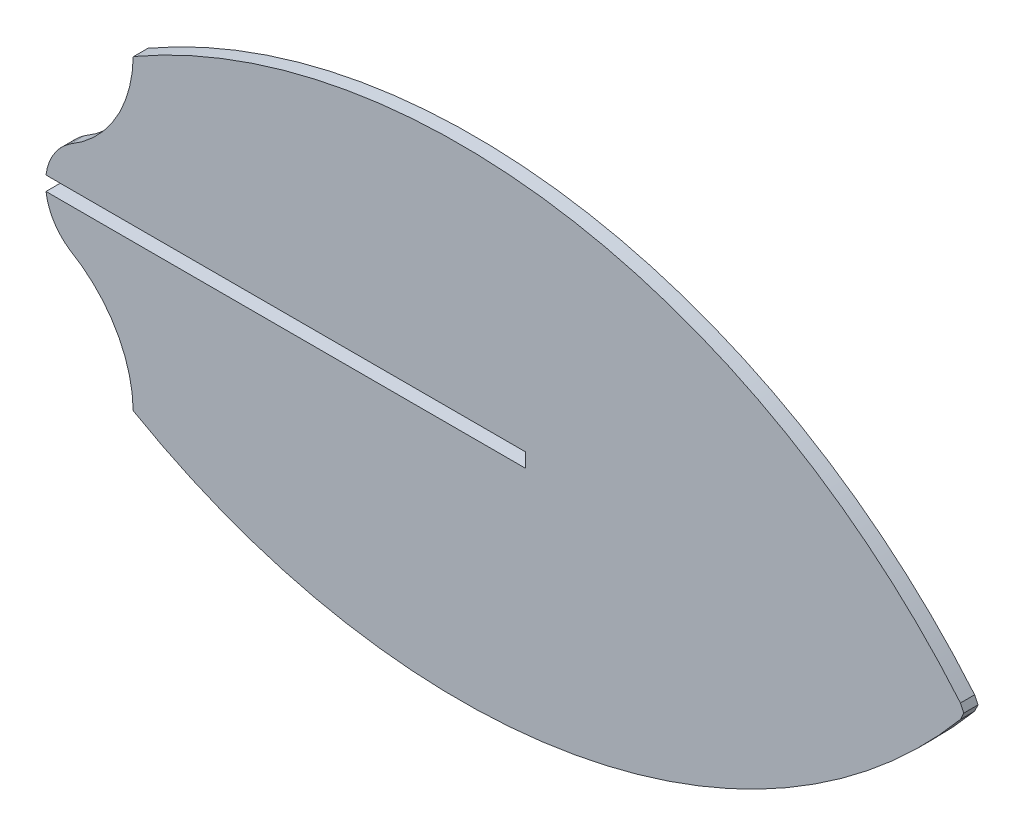
SolidWorks part; units mm, degrees
ref_plane "Front Plane" through (0, 0, 0) normal (0, 0, 1) x (1, 0, 0)
ref_plane "Top Plane" through (0, 0, 0) normal (0, 1, 0) x (1, 0, 0)
ref_plane "Right Plane" through (0, 0, 0) normal (1, 0, 0) x (0, 0, -1)
sketch "Sketch1" plane through (0, 0, 0) normal (0, 0, 1) x (1, 0, 0)
  line L0 (79.3572, 0) -> (79.3572, -1.524)
  line L2 (79.3572, 0) -> (27.9972, 0)
  line L3 (79.3572, -1.524) -> (79.3572, 0) construction
  line L4 (79.3572, -0.762) -> (126.3316, -0.762) construction
  line L5 (126.3316, -0.762) -> (125.9746, 0)
  line L6 (126.3316, -0.762) -> (125.9746, -1.524)
  line L7 (79.3572, -1.524) -> (27.9972, -1.524)
  arc A0 (27.9972, -1.524) -> (30.5853, -5.7032) centre (33.896, -0.762) ccw
  arc A1 (37.3432, -17.1688) -> (37.4005, -17.2275) centre (104.2089, 47.9432) ccw
  arc A2 (37.4005, 15.7035) -> (125.9746, 0) centre (72.3276, -44.9421) cw
  arc A3 (30.5853, -5.7032) -> (37.3432, -17.1688) centre (23.8339, -17.407) cw
  arc A4 (37.4005, -17.2275) -> (125.9746, -1.524) centre (72.3276, 43.4181) ccw
  arc A6 (30.5853, 4.1792) -> (37.3432, 15.6448) centre (23.8339, 15.883) ccw
  arc A7 (37.3432, 15.6448) -> (37.4005, 15.7035) centre (104.2089, -49.4672) cw
  arc A8 (30.5853, 4.1792) -> (27.9972, 0) centre (33.896, -0.762) ccw
extrude "Boss-Extrude1" add sketch "Sketch1" along normal blind 1.524
